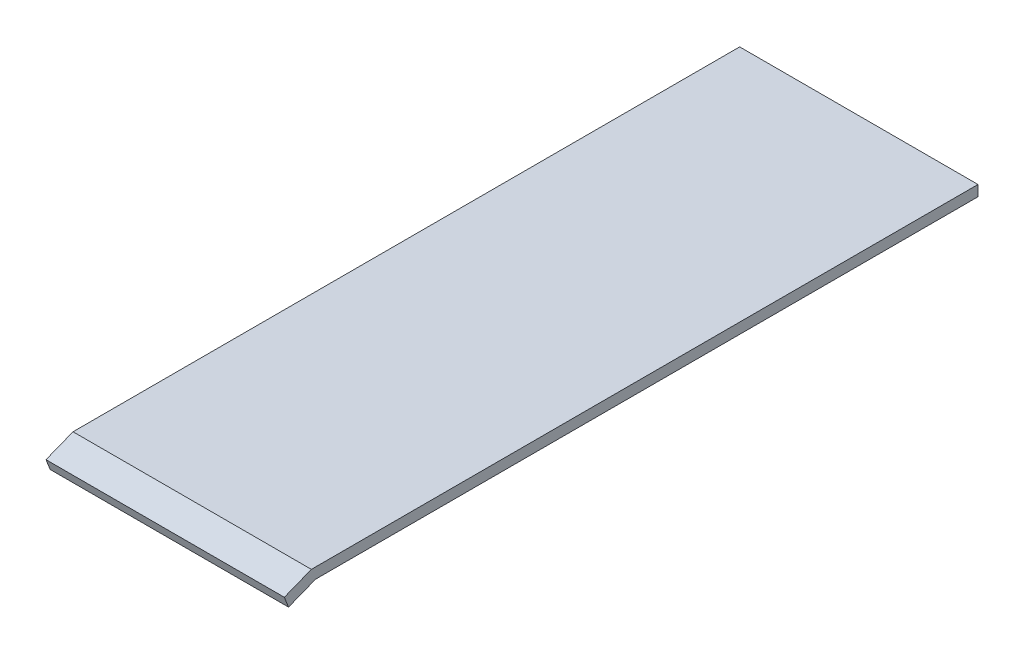
SolidWorks part; units mm, degrees
ref_plane "Front Plane" through (0, 0, 0) normal (0, 0, 1) x (1, 0, 0)
ref_plane "Top Plane" through (0, 0, 0) normal (0, 1, 0) x (1, 0, 0)
ref_plane "Right Plane" through (0, 0, 0) normal (1, 0, 0) x (0, 0, -1)
sketch "Sketch1" plane through (0, 0, 0) normal (0, 1, 0) x (1, 0, 0)
  line L1 (-3.175, -3.175) -> (3.175, -3.175)
  line L2 (-3.175, -3.175) -> (-3.175, 3.175)
  line L3 (-3.175, 3.175) -> (3.175, 3.175)
  line L4 (3.175, -3.175) -> (3.175, 3.175)
  line L5 (-3.175, -3.175) -> (3.175, 3.175) construction
  line L6 (-3.175, 3.175) -> (3.175, -3.175) construction
  point P0 (0, 0)
  dimension "D1" = 6.35
extrude "Boss-Extrude1" add sketch "Sketch1" along normal blind 5.08
sketch "Sketch2" plane through (3.175, 0, 0) normal (1, 0, 0) x (0, 0, -1)
  line L0 (3.175, 5.08) -> (-79.375, 5.08)
  line L1 (-79.375, 5.08) -> (-82.7413, 3.753)
  line L2 (-82.7413, 3.753) -> (-83.2644, 5.08)
  line L3 (-83.2644, 5.08) -> (-79.8981, 6.407)
  line L4 (-79.8981, 6.407) -> (3.175, 6.407)
  line L5 (3.175, 6.407) -> (3.175, 5.08)
  line L6 (-3.175, 5.08) -> (-3.175, 0) construction
  dimension "D1" = 76.2
extrude "Boss-Extrude2" add sketch "Sketch2" against normal blind 14.85 and the other way blind 14.85
